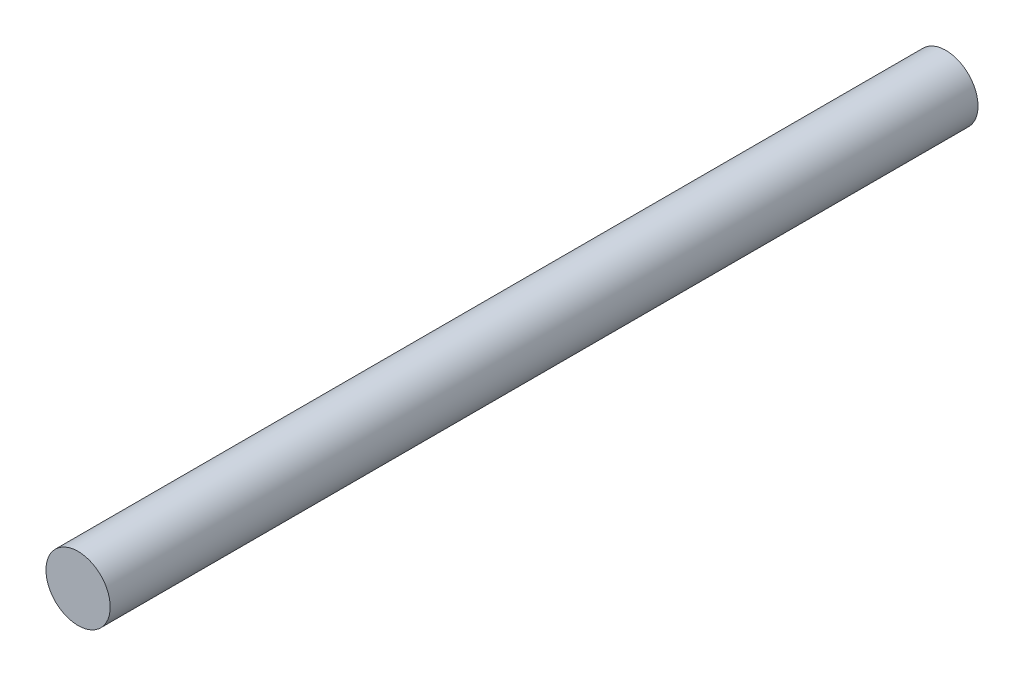
SolidWorks part; units mm, degrees
ref_plane "Front Plane" through (0, 0, 0) normal (0, 0, 1) x (1, 0, 0)
ref_plane "Top Plane" through (0, 0, 0) normal (0, 1, 0) x (1, 0, 0)
ref_plane "Right Plane" through (0, 0, 0) normal (1, 0, 0) x (0, 0, -1)
sketch "Sketch1" plane through (0, 0, 0) normal (0, 0, 1) x (1, 0, 0)
  circle A0 centre (0, 0) radius 2
  dimension "D1" = 4
extrude "Boss-Extrude1" add sketch "Sketch1" along normal blind 54
